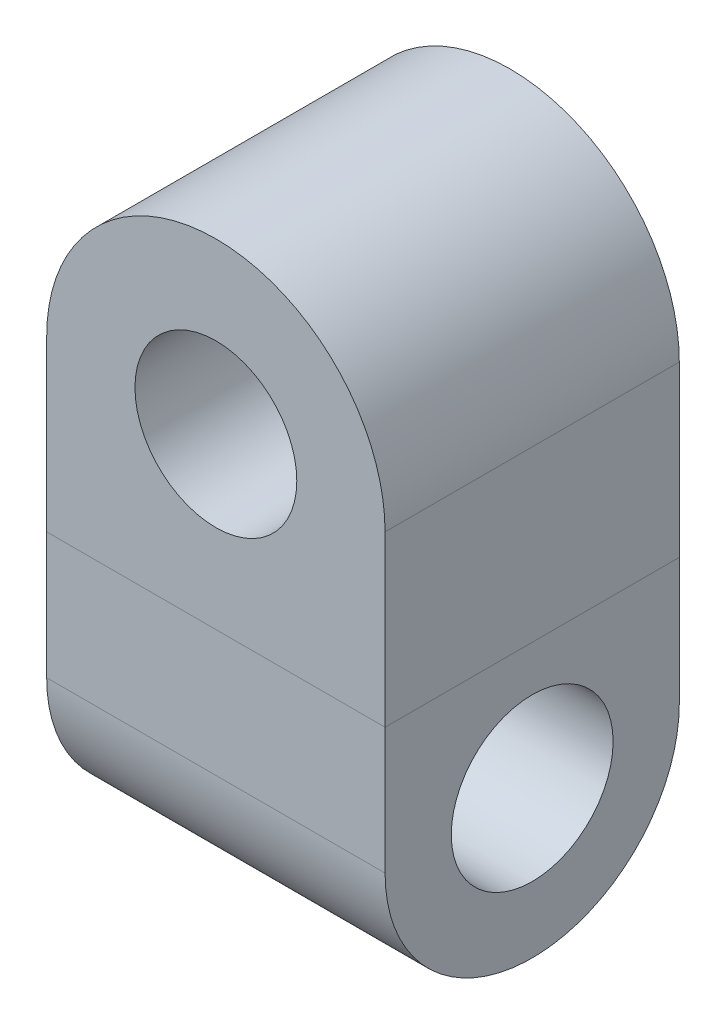
SolidWorks part; units mm, degrees
ref_plane "Front Plane" through (0, 0, 0) normal (0, 0, 1) x (1, 0, 0)
ref_plane "Top Plane" through (0, 0, 0) normal (0, 1, 0) x (1, 0, 0)
ref_plane "Right Plane" through (0, 0, 0) normal (1, 0, 0) x (0, 0, -1)
sketch "Sketch1" plane through (0, 0, 0) normal (0, 0, 1) x (1, 0, 0)
  line L0 (-2.921, 0) -> (-2.921, -2.921)
  line L5 (2.921, 0) -> (2.921, -2.921)
  line L6 (2.921, -2.921) -> (-2.921, -2.921)
  line L8 (2.921, -2.921) -> (2.921, 2.921) construction
  line L9 (2.921, 2.921) -> (0, 2.921) construction
  arc A0 (2.921, 0) -> (-2.921, 0) centre (0, 0) ccw
  circle A1 centre (0, 0) radius 1.397
  point P1 (2.921, 0)
  point P10 (0, 2.921)
  dimension "D1" = 5.842
  dimension "D2" = 2.794
extrude "Boss-Extrude1" add sketch "Sketch1" along normal blind 5.08
sketch "Sketch2" plane through (0, 0, 0) normal (1, 0, 0) x (0, 0, -1)
  line L3 (-5.08, -2.921) -> (0, -2.921)
  line L5 (-5.08, -2.921) -> (-5.08, -8.17) construction
  line L6 (0, -2.921) -> (0, -8.1678) construction
  line L9 (-5.08, 2.921) -> (-5.08, 0) construction
  line L10 (-5.08, -5.1018) -> (-5.08, -2.921)
  line L11 (0, -5.1018) -> (0, -2.921)
  line L13 (-5.08, -2.921) -> (0, -2.921) construction
  circle A0 centre (-2.54, -5.1018) radius 1.397
  arc A2 (-5.08, -5.1018) -> (0, -5.1018) centre (-2.54, -5.1018) ccw
  point P0 (0, -5.1018)
  dimension "D1" = 2.794
extrude "Boss-Extrude2" add sketch "Sketch2" along direction (1, 0, 0) on the side against the normal mid plane 5.842 separate body contours A0 | L10 L3 L11 A2
